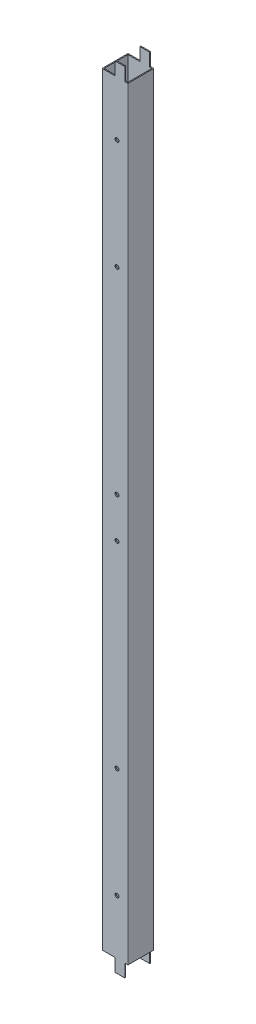
SolidWorks part; units mm, degrees
ref_plane "Front Plane" through (0, 0, 0) normal (0, 0, 1) x (1, 0, 0)
ref_plane "Top Plane" through (0, 0, 0) normal (0, 1, 0) x (1, 0, 0)
ref_plane "Right Plane" through (0, 0, 0) normal (1, 0, 0) x (0, 0, -1)
sketch "Sketch1" plane through (0, 0, 0) normal (0, 1, 0) x (1, 0, 0)
  line L0 (1.5, 1.5) -> (38.5, 1.5)
  line L1 (0.5, 0) -> (39.5, 0)
  line L2 (0, 0.5) -> (0, 39.5)
  line L3 (0.5, 40) -> (39.5, 40)
  line L4 (40, 0.5) -> (40, 39.5)
  line L5 (38.5, 1.5) -> (38.5, 38.5)
  line L6 (1.5, 38.5) -> (38.5, 38.5)
  line L7 (1.5, 1.5) -> (1.5, 38.5)
  arc A0 (39.5, 0) -> (40, 0.5) centre (39.5, 0.5) ccw
  arc A1 (0.5, 0) -> (0, 0.5) centre (0.5, 0.5) cw
  arc A2 (0, 39.5) -> (0.5, 40) centre (0.5, 39.5) cw
  arc A3 (39.5, 40) -> (40, 39.5) centre (39.5, 39.5) cw
  arc A4 (38.5, 1.5) -> (38.5, 1.5) centre (38.5, 1.5) ccw
  arc A5 (38.5, 38.5) -> (38.5, 38.5) centre (38.5, 38.5) cw
  arc A6 (1.5, 38.5) -> (1.5, 38.5) centre (1.5, 38.5) cw
  arc A7 (1.5, 1.5) -> (1.5, 1.5) centre (1.5, 1.5) cw
  point P9 (0, 0)
  dimension "D3" = 0.5
  dimension "D1" = 40
  dimension "D2" = 40
  dimension "D4" = 1.5
extrude "Boss-Extrude1" add sketch "Sketch1" along normal blind 1220
sketch "Sketch2" plane through (0, 0, 0) normal (0, 0, 1) x (1, 0, 0)
  line L10 (20, 1220) -> (20, 1200)
  line L17 (40, 1220) -> (35, 1220)
  line L18 (40, 1220) -> (40, 1200)
  line L19 (40, 1200) -> (35, 1200)
  line L20 (35, 1220) -> (35, 1200)
  line L21 (0.5, 1220) -> (39.5, 1220) construction
  line L26 (0, 610) -> (39.5, 610) construction
  line L27 (0, 1220) -> (0, 0) construction
  line L28 (39.5, 1220) -> (39.5, 0) construction
  line L37 (0, 20) -> (20, 20)
  line L38 (0, 1220) -> (20, 1220)
  line L39 (0, 1220) -> (0, 1200)
  line L40 (0, 1200) -> (20, 1200)
  line L42 (0, 0) -> (0, 20)
  line L43 (0, 0) -> (20, 0)
  line L44 (35, 0) -> (35, 20)
  line L45 (40, 20) -> (35, 20)
  line L46 (40, 0) -> (40, 20)
  line L47 (40, 0) -> (35, 0)
  line L48 (20, 0) -> (20, 20)
  dimension "D1" = 20
  dimension "D2" = 5
  dimension "D3" = 20
extrude "Cut-Extrude1" cut sketch "Sketch2" against normal blind 50
sketch "Sketch3" plane through (0, 0, -40) normal (0, 0, 1) x (1, 0, 0)
  line L0 (0, 1200) -> (0, 20) construction
  line L1 (30, 893.6) -> (20, 893.6)
  line L2 (30, 893.6) -> (30, 891.6)
  line L5 (0, 873.6) -> (13.6425, 873.6) construction
  line L10 (39.5, 610) -> (10, 610) construction
  line L11 (39.5, 1200) -> (39.5, 20) construction
  line L20 (0.5, 1200) -> (20, 1200) construction
  line L21 (30, 891.6) -> (22, 891.6)
  line L25 (22, 891.6) -> (22, 855.6)
  line L26 (22, 855.6) -> (30, 855.6)
  line L27 (30, 855.6) -> (30, 853.6)
  line L28 (30, 853.6) -> (20, 853.6)
  line L29 (20, 893.6) -> (20, 853.6)
  line L30 (20, 326.4) -> (20, 366.4)
  line L31 (30, 366.4) -> (20, 366.4)
  line L32 (30, 364.4) -> (30, 366.4)
  line L33 (22, 364.4) -> (30, 364.4)
  line L34 (22, 328.4) -> (22, 364.4)
  line L35 (30, 328.4) -> (22, 328.4)
  line L36 (30, 326.4) -> (30, 328.4)
  line L37 (30, 326.4) -> (20, 326.4)
  dimension "D1" = 10
  dimension "D2" = 40
  dimension "D3" = 20
  dimension "D4" = 306.4
  dimension "D5" = 2
  dimension "D6" = 2
  dimension "D7" = 20
extrude "Cut-Extrude2" cut sketch "Sketch3" along normal blind 10
sketch "Sketch4" plane through (0, 0, -40) normal (0, 0, -1) x (-1, 0, 0)
  line L0 (-0.5, 610) -> (-39.5, 610) construction
  line L1 (-0.5, 1200) -> (-0.5, 20) construction
  line L2 (-39.5, 1200) -> (-39.5, 20) construction
  line L3 (-30, 703.06) -> (-20, 703.06)
  line L4 (-20, 703.06) -> (-20, 663.06)
  line L5 (-20, 663.06) -> (-30, 663.06)
  line L6 (-30, 663.06) -> (-30, 665.06)
  line L7 (-30, 665.06) -> (-22, 665.06)
  line L8 (-22, 665.06) -> (-22, 701.06)
  line L9 (-22, 701.06) -> (-30, 701.06)
  line L10 (-30, 701.06) -> (-30, 703.06)
  line L11 (-40, 1200) -> (-40, 20) construction
  line L12 (-30, 518.94) -> (-30, 516.94)
  line L13 (-22, 518.94) -> (-30, 518.94)
  line L14 (-22, 554.94) -> (-22, 518.94)
  line L15 (-30, 554.94) -> (-22, 554.94)
  line L16 (-30, 556.94) -> (-30, 554.94)
  line L17 (-20, 556.94) -> (-30, 556.94)
  line L18 (-20, 516.94) -> (-20, 556.94)
  line L19 (-30, 516.94) -> (-20, 516.94)
  dimension "D1" = 40
  dimension "D2" = 10
  dimension "D3" = 2
  dimension "D4" = 2
  dimension "D5" = 20
  dimension "D6" = 53.06
  dimension "D7" = 2
extrude "Cut-Extrude3" cut sketch "Sketch4" against normal blind 10
sketch "Sketch5" plane through (0, 0, -40) normal (0, 0, -1) x (-1, 0, 0)
  line L0 (0, 1200) -> (0, 20) construction
  line L1 (-0.5, 1200) -> (-20, 1200) construction
  line L2 (-0.5, 610) -> (-39.5, 610) construction
  line L3 (-0.5, 1200) -> (-0.5, 20) construction
  line L4 (-39.5, 1200) -> (-39.5, 20) construction
  circle A0 centre (-23, 1115.75) radius 3
  circle A1 centre (-23, 945.75) radius 3
  circle A2 centre (-23, 641) radius 3
  circle A3 centre (-23, 579) radius 3
  circle A4 centre (-23, 274.25) radius 3
  circle A5 centre (-23, 104.25) radius 3
  point P22 (0, 0)
  point P23 (0, 0)
  dimension "D1" = 23
  dimension "D2" = 6
  dimension "D3" = 84.25
  dimension "D4" = 170
  dimension "D5" = 559
extrude "Cut-Extrude4" cut sketch "Sketch5" against normal through all
